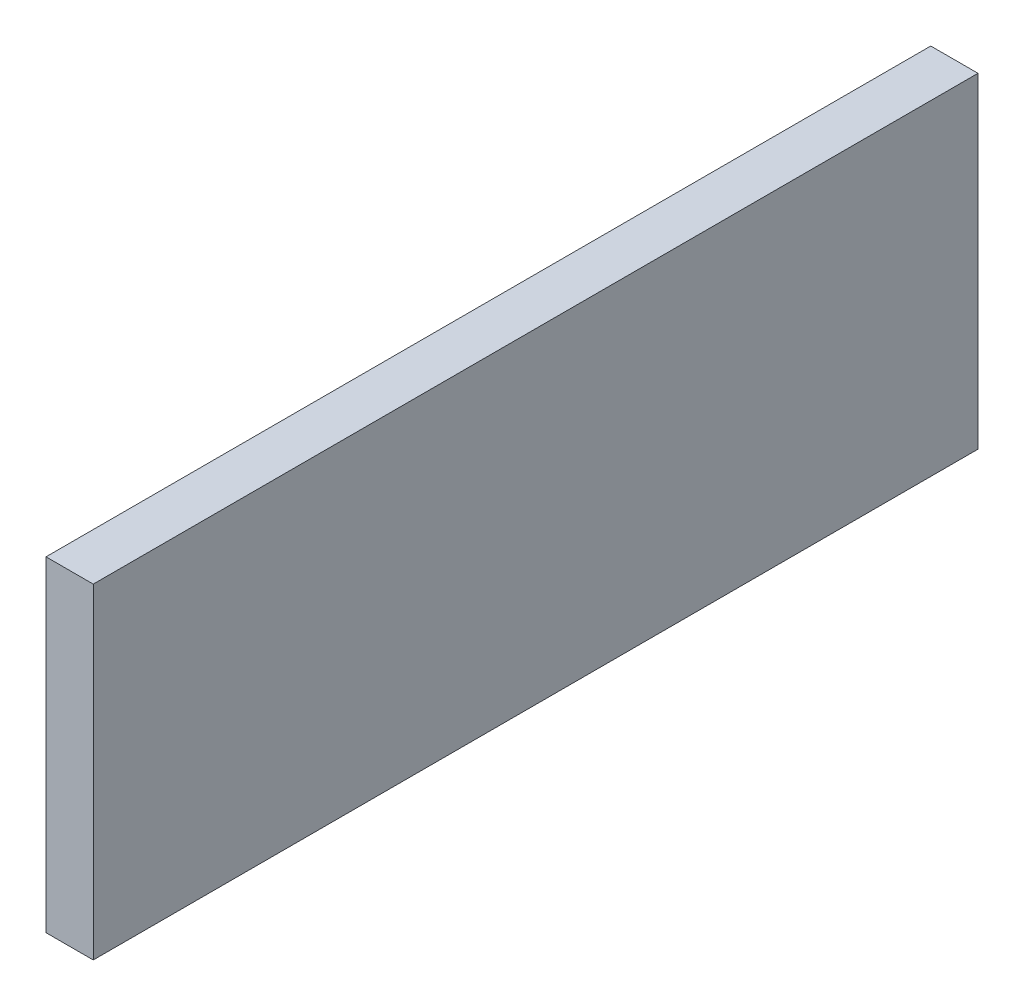
SolidWorks part; units mm, degrees
ref_plane "Спереди" through (0, 0, 0) normal (0, 0, 1) x (1, 0, 0)
ref_plane "Сверху" through (0, 0, 0) normal (0, 1, 0) x (1, 0, 0)
ref_plane "Справа" through (0, 0, 0) normal (1, 0, 0) x (0, 0, -1)
sketch "Эскиз1" plane through (0, 0, 0) normal (1, 0, 0) x (0, 0, -1)
  line L1 (-31.6515, 15.6735) -> (305.3485, 15.6735)
  line L2 (-31.6515, 15.6735) -> (-31.6515, -108.3265)
  line L3 (-31.6515, -108.3265) -> (305.3485, -108.3265)
  line L4 (305.3485, 15.6735) -> (305.3485, -108.3265)
  dimension "D1" = 337
  dimension "D2" = 124
extrude "Бобышка-Вытянуть1" add sketch "Эскиз1" along normal blind 18
